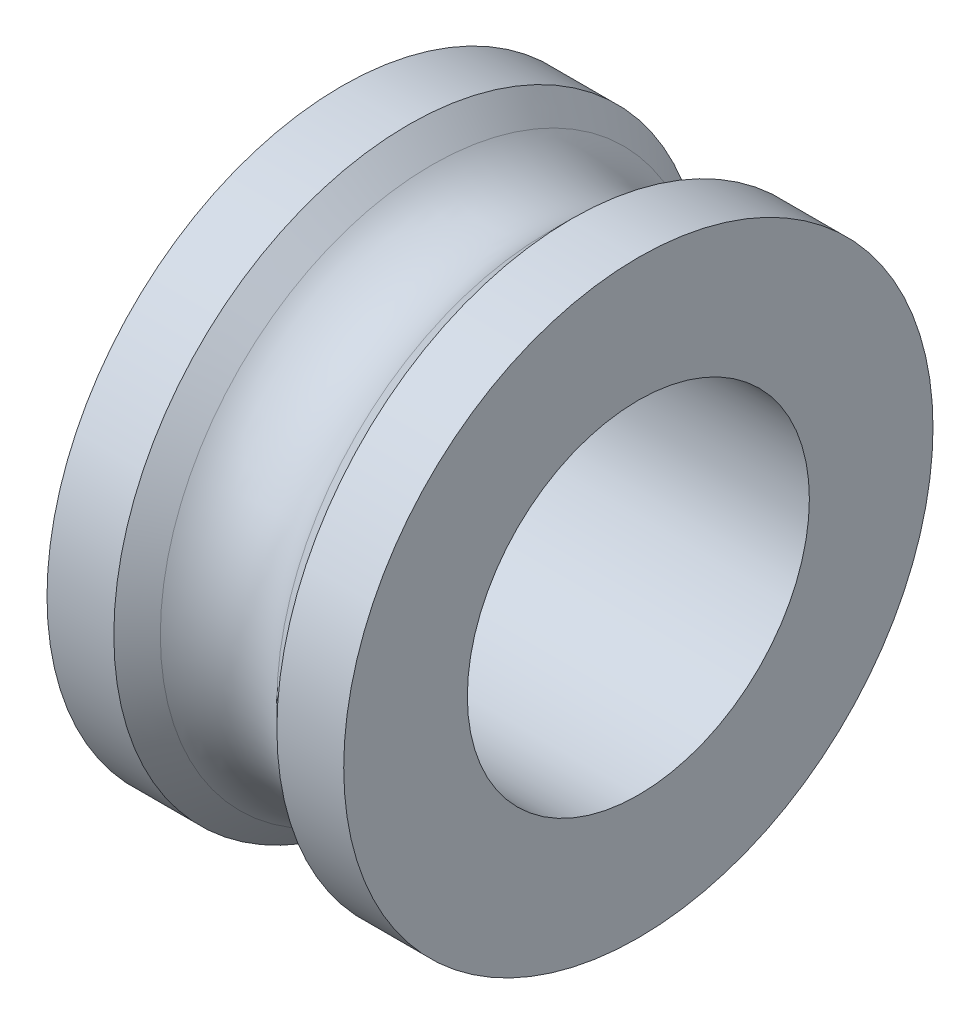
SolidWorks part; units mm, degrees
ref_plane "Vorne" through (0, 0, 0) normal (0, 0, 1) x (1, 0, 0)
ref_plane "Oben" through (0, 0, 0) normal (0, 1, 0) x (1, 0, 0)
ref_plane "Rechts" through (0, 0, 0) normal (1, 0, 0) x (0, 0, -1)
sketch "Skizze1" plane through (0, 0, 0) normal (0, 0, 1) x (1, 0, 0)
  line L0 (12.1559, 0) -> (-12.1559, 0) construction
  line L1 (-1.8, 2.075) -> (1.8, 2.075)
  line L2 (1.8, 2.075) -> (1.8, 3.575)
  line L3 (1.8, 3.575) -> (0.9892, 3.575)
  line L4 (0.9892, 3.575) -> (0.7071, 3.2929)
  line L5 (-0.7071, 3.2929) -> (-0.9892, 3.575)
  line L6 (-0.9892, 3.575) -> (-1.8, 3.575)
  line L7 (-1.8, 3.575) -> (-1.8, 2.075)
  arc A0 (-0.7071, 3.2929) -> (0.7071, 3.2929) centre (0, 4) ccw
  dimension "D1" = 1
  dimension "D2" = 3.6
  dimension "D3" = 1.5
  dimension "D4" = 90
  dimension "D5" = 4.15
  dimension "D6" = 6
  dimension "D7" = 0.925
revolve "Rotation1" add sketch "Skizze1" angle 360 about L0
move or copy body "Körper-Verschieben/Kopieren1" [suppressed] bodies to move or copy 103
